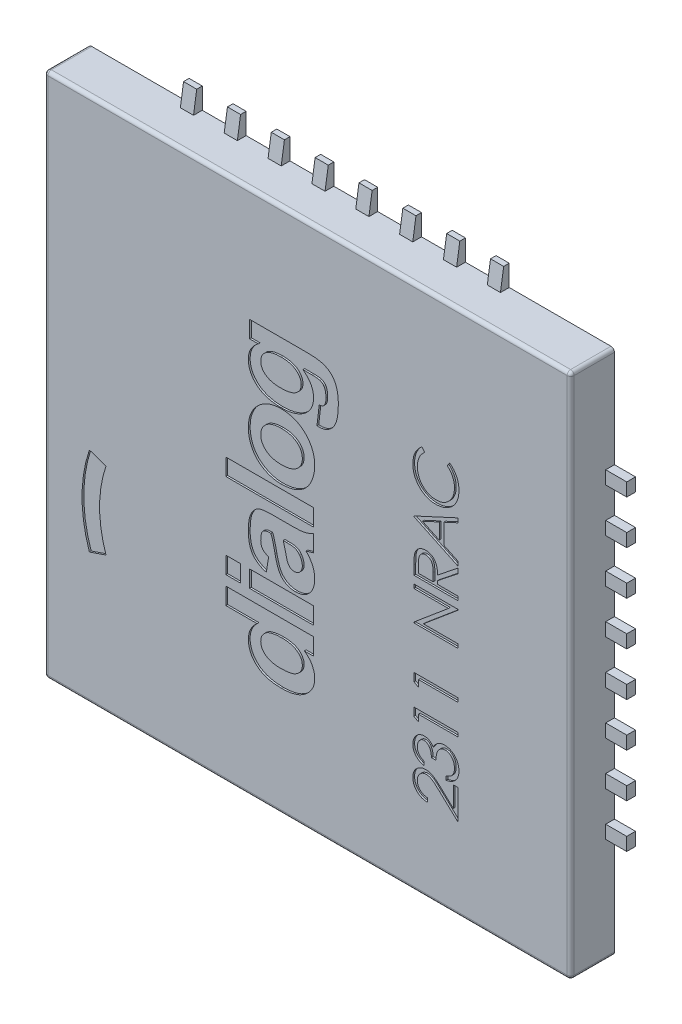
SolidWorks part; units mm, degrees
ref_plane "Płaszczyzna przednia" through (0, 0, 0) normal (0, 0, 1) x (1, 0, 0)
ref_plane "Płaszczyzna górna" through (0, 0, 0) normal (0, 1, 0) x (1, 0, 0)
ref_plane "Płaszczyzna prawa" through (0, 0, 0) normal (1, 0, 0) x (0, 0, -1)
sketch "Sketch1" plane through (0, 0, 0) normal (0, 0, 1) x (1, 0, 0)
  line L1 (3, -3) -> (-3, -3)
  line L2 (3, -3) -> (3, 3)
  line L3 (3, 3) -> (-3, 3)
  line L4 (-3, -3) -> (-3, 3)
  line L5 (3, -3) -> (-3, 3) construction
  line L6 (3, 3) -> (-3, -3) construction
  point P0 (0, 0)
  dimension "D1" = 6
extrude "Boss-Extrude1" add sketch "Sketch1" along normal blind 0.5
sketch "Sketch2" plane through (0, 0, 0.5) normal (0, 0, 1) x (1, 0, 0)
  line L0 (0.0692, -3) -> (0.0692, 3) construction
  line L1 (-3, -3) -> (3, -3) construction
  line L2 (3, 3) -> (-3, 3) construction
  line L3 (-2.2979, -1.4411) -> (-2.4871, -1.5058)
  line L4 (-2.2979, -0.5625) -> (-2.4871, -0.4978)
  line L7 (1.7138, -2.0888) -> (1.7138, 1.0025) construction
  arc A0 (-2.4871, -1.5058) -> (-2.4871, -0.4978) centre (-1.0138, -1.0018) cw
  arc A1 (-2.2979, -1.4411) -> (-2.2979, -0.5625) centre (-1.0138, -1.0018) cw
  text T0 "dialog" font "Century Gothic" height 1
  text T1 "2311  NRAC" font "Century Gothic" height 0.5
  dimension "D1" = 0.2
extrude "Cut-Extrude1" cut sketch "Sketch2" against normal blind 0.02
sketch "Sketch3" plane through (0, 0, 0) normal (0, 0, -1) x (-1, 0, 0)
  line L0 (3, -3) -> (1.8, -3) construction
  line L1 (3, -3) -> (-3, -3) construction
  line L2 (1.8, -3) -> (1.8, -3.24)
  line L3 (1.8, -3.24) -> (1.65, -3.24)
  line L4 (1.65, -3.24) -> (1.65, -3)
  line L5 (1.65, -3) -> (1.8, -3)
  dimension "D1" = 0.24
  dimension "D2" = 0.15
extrude "Boss-Extrude2" add sketch "Sketch3" against normal blind 0.1 separate body
pattern_linear "LPattern1" count 8 spacing 0.5 along (1, 0, 0) of bodies 103
sketch "Sketch4" plane through (0, 0, 0) normal (0, 0, -1) x (-1, 0, 0)
  circle A0 centre (0, 0) radius 0.5449
extrude "Boss-Extrude3" add sketch "Sketch4" along normal blind 0.1 separate body
pattern_circular "CirPattern1" count 4 over 360 about axis through (0, 0, 0) along (0, 0, 1) of bodies 103 104 106 105 107 108 109 110
fillet "Fillet3" radius 0.04 4 edges at (-3, 3, 0.25) (3, 3, 0.25) (3, -3, 0.25) (-3, -3, 0.25)
fillet "Fillet4" radius 0.04 8 edges at (-2.9883, -2.9883, 0.5) (-3, 0, 0.5) (-2.9883, 2.9883, 0.5) (0, 3, 0.5) (2.9883, 2.9883, 0.5) (3, 0, 0.5) (2.9883, -2.9883, 0.5) (0, -3, 0.5)
sketch "Szkic1" plane through (1.85, 0, 0) normal (1, 0, 0) x (0, 0, -1)
  line L0 (-0.1, -3) -> (-0.0634, -3.24)
  line L1 (-0.1, -3.24) -> (0, -3.24) construction
  line L2 (-0.0634, -3.24) -> (-0.1, -3.24)
  line L3 (-0.1, -3.24) -> (-0.1, -3)
  line L4 (-0.46, 0) -> (-0.9126, 0) construction
  line L5 (-0.46, 2.96) -> (-0.46, -2.96) construction
  line L6 (-0.1, 3.24) -> (-0.1, 3)
  line L7 (-0.0634, 3.24) -> (-0.1, 3.24)
  line L8 (-0.1, 3) -> (-0.0634, 3.24)
extrude "Wytnij-wyciągnięcie1" cut sketch "Szkic1" against normal through all
